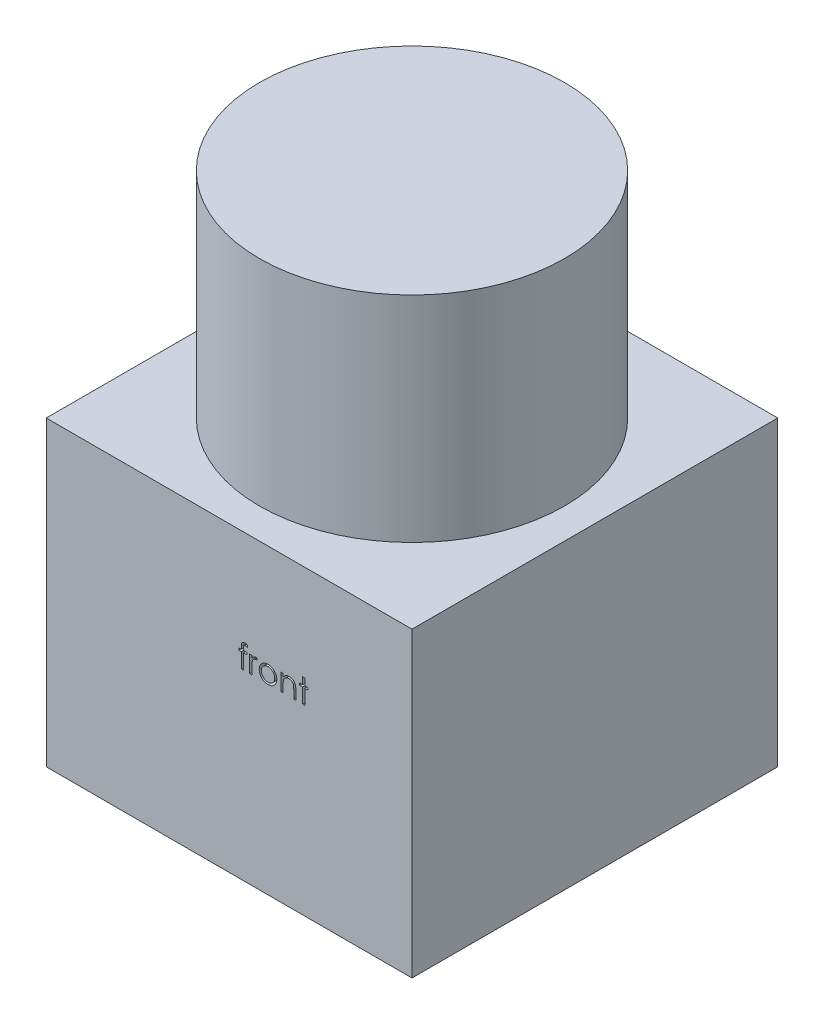
SolidWorks part; units mm, degrees
ref_plane "Front Plane" through (0, 0, 0) normal (0, 0, 1) x (1, 0, 0)
ref_plane "Top Plane" through (0, 0, 0) normal (0, 1, 0) x (1, 0, 0)
ref_plane "Right Plane" through (0, 0, 0) normal (1, 0, 0) x (0, 0, -1)
sketch "Sketch1" plane through (0, 0, 0) normal (0, 0, 1) x (1, 0, 0)
  line L1 (0, 0) -> (50, 0)
  line L2 (0, 0) -> (0, 41.3)
  line L3 (0, 41.3) -> (50, 41.3)
  line L4 (50, 0) -> (50, 41.3)
  dimension "D1" = 50
  dimension "D2" = 41.3
extrude "Boss-Extrude1" add sketch "Sketch1" along normal blind 50
sketch "Sketch2" plane through (0, 41.3, 0) normal (0, 1, 0) x (1, 0, 0)
  circle A0 centre (25, -25) radius 20.85
  dimension "D1" = 41.7
extrude "Boss-Extrude2" add sketch "Sketch2" along normal blind 29.3
sketch "Sketch3" plane through (0, 0, 0) normal (0, -1, 0) x (1, 0, 0)
  line L0 (45.864, 45.864) -> (47.564, 45.864)
  line L1 (50, 50) -> (0, 0) construction
  line L2 (4.136, 4.136) -> (2.436, 4.136) construction
  circle A0 centre (45.864, 45.864) radius 1.7
  circle A1 centre (4.136, 4.136) radius 1.7
  point P9 (0, 0)
  dimension "D1" = 1.7
  dimension "D2" = 4.8
  dimension "D3" = 1.7
  dimension "D4" = 4.8
extrude "Cut-Extrude1" cut sketch "Sketch3" against normal blind 12.7 contours A0 | A1
sketch "Sketch4" plane through (0, 0, 50) normal (0, 0, 1) x (1, 0, 0)
  text T0 "front"
extrude "Cut-Extrude2" cut sketch "Sketch4" against normal blind 2.54
ref_plane "Plane1" through (0, 0, 25) normal (0, 0, 1) x (1, 0, 0)
ref_plane "Plane2" through (25, 0, 0) normal (1, 0, 0) x (0, 0, -1)
